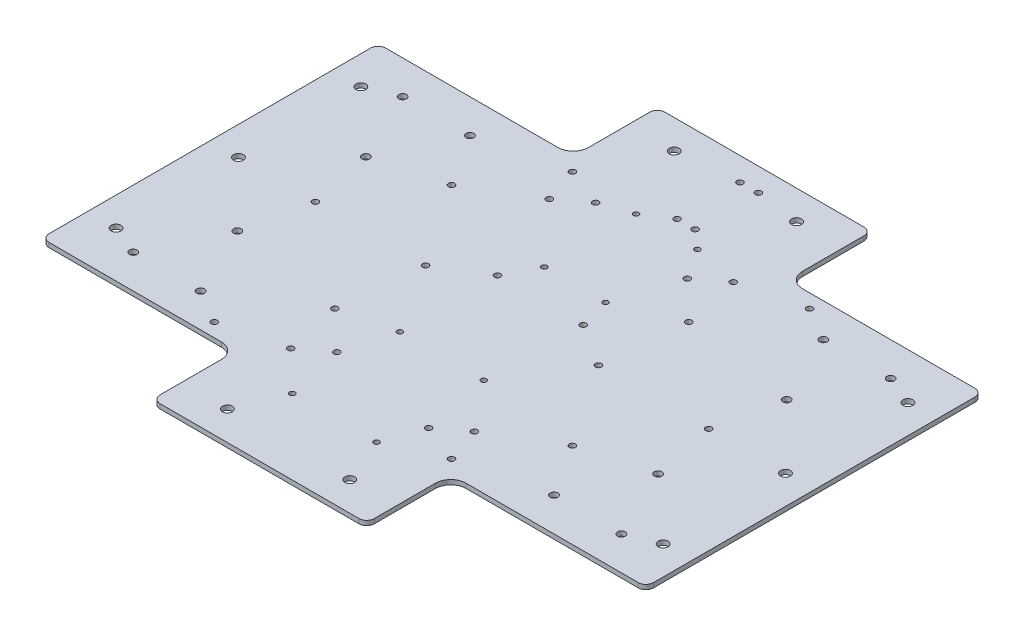
SolidWorks part; units mm, degrees
material "1060 Сплав"
ref_plane "Спереди" through (0, 0, 0) normal (0, 0, 1) x (1, 0, 0)
ref_plane "Сверху" through (0, 0, 0) normal (0, 1, 0) x (1, 0, 0)
ref_plane "Справа" through (0, 0, 0) normal (1, 0, 0) x (0, 0, -1)
sketch "Эскиз1" plane through (0, 0, 0) normal (0, 1, 0) x (1, 0, 0)
  line L1 (-65, -165) -> (65, -165)
  line L2 (-197.5, -105) -> (-197.5, 105)
  line L3 (-65, 165) -> (65, 165)
  line L4 (197.5, -105) -> (197.5, 105)
  line L5 (197.5, -105) -> (137.5, -105) construction
  line L6 (137.5, -110) -> (137.5, -66.2968) construction
  line L18 (-284.5497, 0) -> (284.3305, 0) construction
  line L19 (-160.9018, 110) -> (-134.9018, 110)
  line L39 (-70, 120) -> (-70, 160)
  line L40 (0, 262.7398) -> (0, -186.5795) construction
  line L41 (-192.5, 110) -> (-80, 110)
  line L43 (-192.5, -110) -> (-80, -110)
  line L44 (-70, -120) -> (-70, -160)
  line L45 (70, 120) -> (70, 160)
  line L46 (192.5, 110) -> (80, 110)
  line L47 (192.5, -110) -> (80, -110)
  line L48 (70, -120) -> (70, -160)
  line L54 (160.9018, -110) -> (134.9018, -110)
  line L60 (160.9018, 110) -> (134.9018, 110)
  line L65 (40, -146) -> (-40, -146) construction
  line L66 (-178.7687, -80) -> (-178.7687, 80) construction
  arc A0 (70, -120) -> (80, -110) centre (80, -120) cw
  arc A1 (70, 120) -> (80, 110) centre (80, 120) ccw
  arc A2 (-80, -110) -> (-70, -120) centre (-80, -120) cw
  arc A3 (-70, 120) -> (-80, 110) centre (-80, 120) cw
  arc A4 (192.5, -110) -> (197.5, -105) centre (192.5, -105) ccw
  arc A5 (70, -160) -> (65, -165) centre (65, -160) cw
  arc A6 (-70, -160) -> (-65, -165) centre (-65, -160) ccw
  arc A7 (-192.5, -110) -> (-197.5, -105) centre (-192.5, -105) cw
  arc A8 (-192.5, 110) -> (-197.5, 105) centre (-192.5, 105) ccw
  arc A9 (197.5, 105) -> (192.5, 110) centre (192.5, 105) ccw
  arc A10 (70, 160) -> (65, 165) centre (65, 160) ccw
  arc A11 (-70, 160) -> (-65, 165) centre (-65, 160) cw
  circle A12 centre (40, 146) radius 3.2
  circle A13 centre (40, -146) radius 3.2
  circle A14 centre (-40, -146) radius 3.2
  circle A15 centre (-40, 146) radius 3.2
  circle A16 centre (-178.7687, 80) radius 3.2
  circle A17 centre (-178.7687, -80) radius 3.2
  circle A18 centre (-178.7687, 0) radius 3.2
  circle A19 centre (178.7687, 80) radius 3.2
  circle A20 centre (178.7687, 0) radius 3.2
  circle A21 centre (178.7687, -80) radius 3.2
  circle A22 centre (137.5, -42) radius 2.5
  circle A23 centre (159.5, -88) radius 2.5
  circle A24 centre (115.5, -88) radius 2.5
  circle A25 centre (-159.5, -88) radius 2.5
  circle A26 centre (-137.5, -42) radius 2.5
  circle A27 centre (-115.5, -88) radius 2.5
  circle A28 centre (159.5, 88) radius 2.5
  circle A29 centre (137.5, 42) radius 2.5
  circle A30 centre (115.5, 88) radius 2.5
  circle A31 centre (-115.5, 88) radius 2.5
  circle A32 centre (-137.5, 42) radius 2.5
  circle A33 centre (-159.5, 88) radius 2.5
  point P0 (0, 0)
  point P3 (70, -110)
  point P17 (-147.9018, 110)
  point P18 (-147.9018, 110)
  point P46 (70, 110)
  point P52 (-70, -110)
  point P55 (-70, 110)
  point P56 (-147.9018, 0)
  point P59 (-178.7687, 0)
  point P62 (178.7687, 80)
  point P77 (197.5, -110)
  point P80 (70, -165)
  point P83 (-70, -165)
  point P86 (-197.5, -110)
  point P89 (-197.5, 110)
  point P92 (197.5, 110)
  point P95 (70, 165)
  point P98 (-70, 165)
  point P99 (178.7687, 0)
  point P100 (40, 146)
  point P101 (178.7687, -80)
  point P103 (-40, 146)
  dimension "D2" = 19
  dimension "D6" = 10
  dimension "D11" = 40
  dimension "D12" = 40
  dimension "D4" = 5
  dimension "D17" = 5
  dimension "D9" = 6.4
  dimension "D3" = 38
  dimension "D14" = 5
  dimension "D5" = 330
  dimension "D7" = 395
  dimension "D8" = 68
  dimension "D10" = 60
  dimension "D13" = 22
  dimension "D15" = 80
  dimension "D16" = 80
  dimension "D18" = 18.7313
  dimension "D19" = 19
  dimension "D20" = 140
extrude "Бобышка-Вытянуть1" add sketch "Эскиз1" along normal blind 3 separate body
sketch "Эскиз2" plane through (0, 3, 0) normal (0, 1, 0) x (1, 0, 0)
  line L0 (197.5, 0) -> (-197.5, 0) construction
  line L1 (197.5, -105) -> (197.5, 105) construction
  line L2 (-197.5, -105) -> (-197.5, 105) construction
  line L3 (0, 165) -> (0, -165) construction
  line L4 (-65, 165) -> (65, 165) construction
  line L5 (-65, -165) -> (65, -165) construction
  line L6 (192.5, 110) -> (80, 110) construction
  circle A0 centre (128.5, 0) radius 2
  circle A1 centre (56.5, 0) radius 2
  circle A2 centre (93.5, 101) radius 2
  circle A3 centre (61.5, 54) radius 2
  circle A4 centre (49.5, 74) radius 2 construction
  circle A5 centre (53.5, 91.0922) radius 2
  circle A6 centre (36.503, 78.0468) radius 2
  circle A7 centre (28.6809, 17.8719) radius 2
  circle A8 centre (-27.3191, 17.8719) radius 2
  circle A9 centre (27.4963, -46.0223) radius 1.75
  circle A10 centre (93.5, -54.0533) radius 2
  circle A11 centre (61.5, -101.043) radius 2
  circle A12 centre (53.5, -78.0725) radius 2
  circle A13 centre (36.503, -90.9991) radius 2
  circle A14 centre (27.4963, -116.0332) radius 1.75
  circle A15 centre (-27.5526, -116.0332) radius 1.75
  circle A16 centre (-27.3191, -46) radius 1.75
  circle A17 centre (-53.6363, -90.9991) radius 2
  circle A18 centre (-36.4017, -78.0725) radius 2
  circle A19 centre (-93.5268, -101.043) radius 2
  circle A20 centre (-61.7277, -54.0533) radius 2
  circle A21 centre (-36.4017, 91.0922) radius 2
  circle A22 centre (-53.6363, 78.0468) radius 2
  circle A23 centre (-61.5417, 101) radius 2
  circle A24 centre (-93.5268, 54) radius 2
  circle A25 centre (-128.5, 0) radius 2
  circle A26 centre (-56.5, 0) radius 2
  circle A27 centre (-16.8323, 37.8725) radius 1.75
  circle A28 centre (-16.7978, 97.9276) radius 1.75
  circle A29 centre (23.276, 97.9276) radius 1.75
  circle A30 centre (23.276, 37.8725) radius 1.75
  circle A31 centre (-0.7596, 149.7308) radius 2
  circle A32 centre (11.1374, 149.8644) radius 2
  circle A33 centre (11.1374, 108.5129) radius 2
  circle A34 centre (-0.6279, 108.5129) radius 2
  point P15 (97.5, 105)
  point P19 (57.5, 50)
  point P24 (53.5, 101)
  point P25 (52.5, 81)
  dimension "D1" = 69
  dimension "D2" = 4
  dimension "D6" = 4
  dimension "D11" = 4
  dimension "D16" = 4
  dimension "D4" = 100
  dimension "D5" = 5
  dimension "D7" = 4
  dimension "D8" = 4
  dimension "D9" = 51
  dimension "D10" = 36
  dimension "D12" = 4
  dimension "D13" = 4
  dimension "D14" = 31
  dimension "D15" = 1
  dimension "D17" = 7
  dimension "D18" = 3
  dimension "D3" = 2
extrude "Вырез-Вытянуть1" cut sketch "Эскиз2" against normal blind 10
